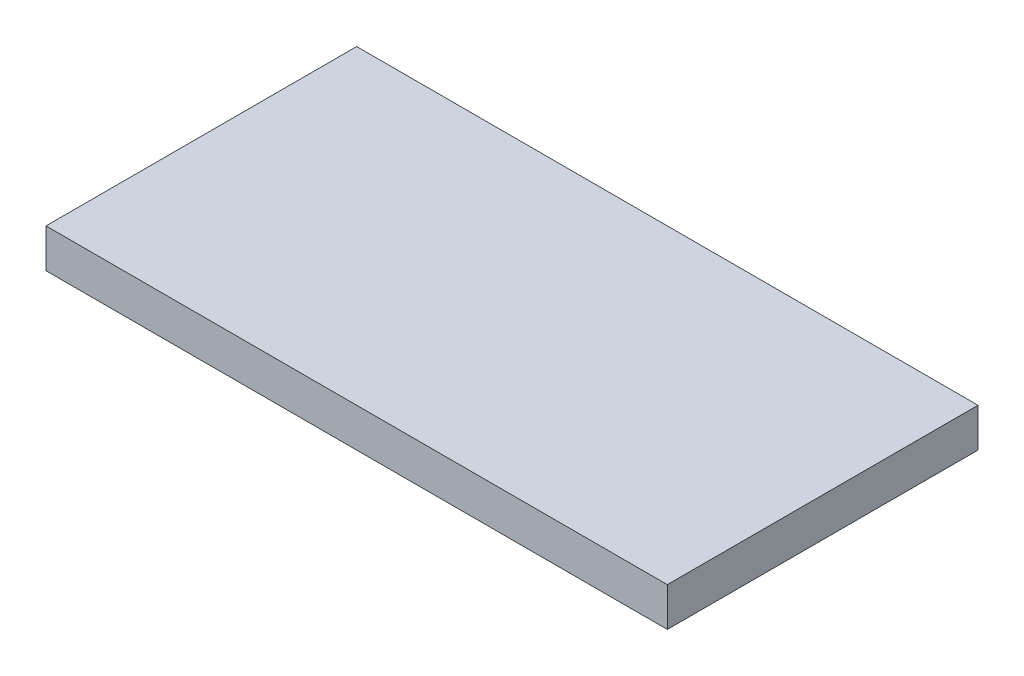
SolidWorks part; units mm, degrees
material "Polyurethane Foam Rigid"
ref_plane "Front Plane" through (0, 0, 0) normal (0, 0, 1) x (1, 0, 0)
ref_plane "Top Plane" through (0, 0, 0) normal (0, 1, 0) x (1, 0, 0)
ref_plane "Right Plane" through (0, 0, 0) normal (1, 0, 0) x (0, 0, -1)
sketch "Sketch1" plane through (0, 0, 0) normal (0, 1, 0) x (1, 0, 0)
  line L1 (-203.2, 101.6) -> (203.2, 101.6)
  line L2 (-203.2, 101.6) -> (-203.2, -101.6)
  line L3 (-203.2, -101.6) -> (203.2, -101.6)
  line L4 (203.2, 101.6) -> (203.2, -101.6)
  point P4 (0, 101.6)
  point P6 (-203.2, 0)
  dimension "D1" = 406.4
  dimension "D2" = 203.2
extrude "Boss-Extrude1" add sketch "Sketch1" along normal mid plane 25.4
